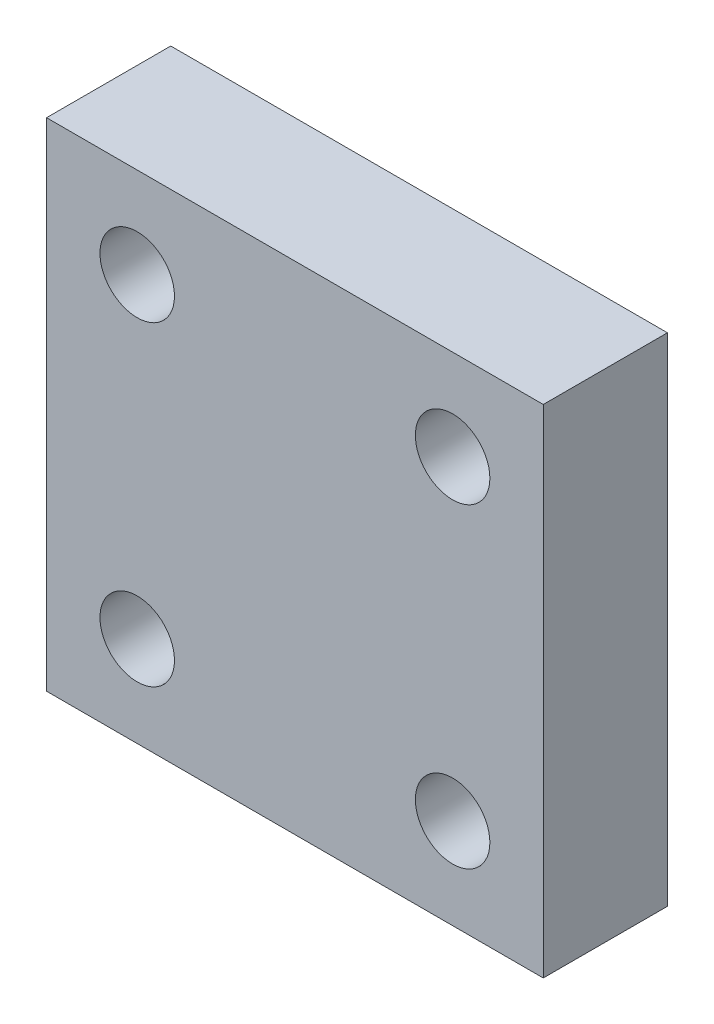
SolidWorks part; units mm, degrees
ref_plane "Front Plane" through (0, 0, 0) normal (0, 0, 1) x (1, 0, 0)
ref_plane "Top Plane" through (0, 0, 0) normal (0, 1, 0) x (1, 0, 0)
ref_plane "Right Plane" through (0, 0, 0) normal (1, 0, 0) x (0, 0, -1)
sketch "Sketch1" plane through (0, 0, 0) normal (0, 0, 1) x (1, 0, 0)
  line L1 (0, 0) -> (-40, 0)
  line L2 (0, 0) -> (0, -40)
  line L3 (0, -40) -> (-40, -40)
  line L4 (-40, 0) -> (-40, -40)
  dimension "D1" = 40
  dimension "D2" = 40
extrude "Boss-Extrude1" add sketch "Sketch1" along normal blind 10
sketch "Sketch2" plane through (0, 0, 0) normal (0, 0, 1) x (1, 0, 0)
  line L4 (-40, 0) -> (-40, -40) construction
  line L6 (-40, -40) -> (0, -40) construction
  circle A6 centre (-35.87, -35.875) radius 1.32
  circle A7 centre (-4.12, -35.875) radius 1.32
  circle A8 centre (-4.12, -4.125) radius 1.32
  circle A9 centre (-35.87, -4.125) radius 1.32
  dimension "D1" = 31.75
  dimension "D2" = 31.75
  dimension "D3" = 4.13
  dimension "D4" = 2.64
  dimension "D5" = 4.125
  dimension "D6" = 2
  dimension "D7" = 2
extrude "Cut-Extrude2" cut sketch "Sketch2" along normal blind 5
sketch "Sketch5" plane through (0, 0, 10) normal (0, 0, 1) x (1, 0, 0)
  line L0 (-40, 0) -> (-40, -40) construction
  line L1 (0, 0) -> (-40, 0) construction
  circle A0 centre (-32.7, -7.3) radius 3
  circle A1 centre (-7.3, -7.3) radius 3
  circle A2 centre (-7.3, -32.7) radius 3
  circle A3 centre (-32.7, -32.7) radius 3
  dimension "D1" = 6
  dimension "D2" = 7.3
  dimension "D3" = 7.3
  dimension "D6" = 25.4
  dimension "D4" = 2
  dimension "D5" = 2
extrude "Cut-Extrude3" cut sketch "Sketch5" against normal blind 5
equation "\"hole_screw_1_4_20\"=6"
equation "\"D1@Sketch5\"=\"hole_screw_1_4_20\""
